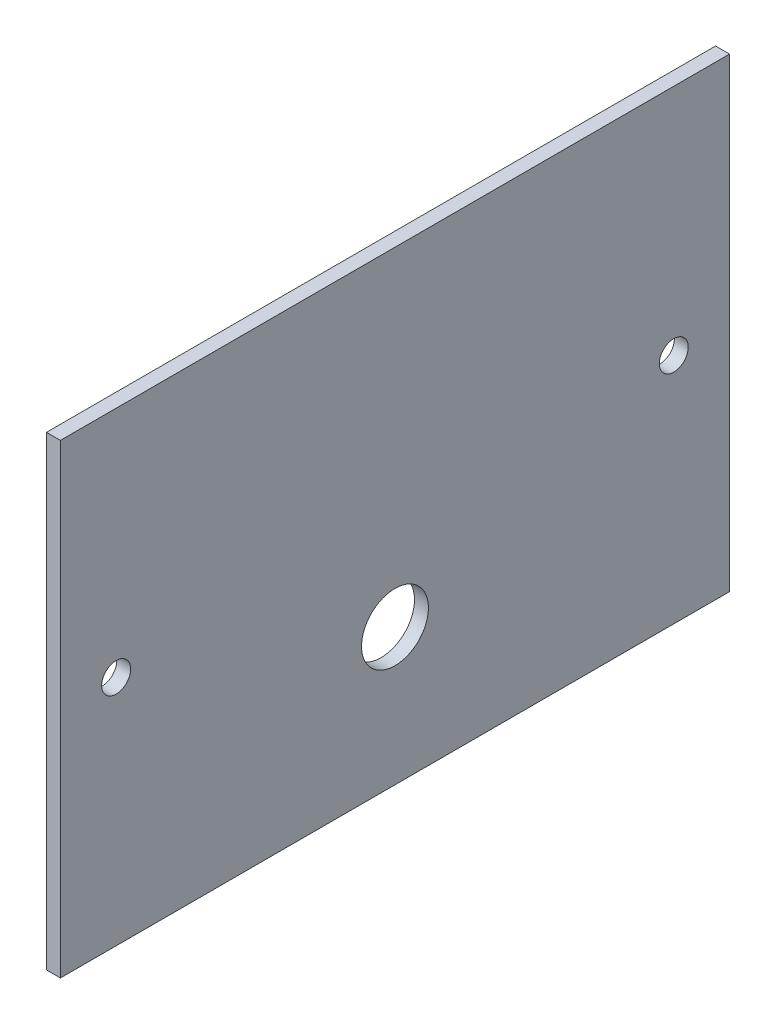
SolidWorks part; units mm, degrees
ref_plane "Front" through (0, 0, 0) normal (0, 0, 1) x (1, 0, 0)
ref_plane "Top" through (0, 0, 0) normal (0, 1, 0) x (1, 0, 0)
ref_plane "Right" through (0, 0, 0) normal (1, 0, 0) x (0, 0, -1)
sketch "Sketch1" plane through (0, 0, 0) normal (1, 0, 0) x (0, 0, -1)
  line L0 (25.4, 106.045) -> (25.4, 0) construction
  line L1 (0, 0) -> (152.4, 0)
  line L2 (0, 0) -> (0, 106.045)
  line L3 (0, 106.045) -> (152.4, 106.045)
  line L4 (152.4, 0) -> (152.4, 106.045)
  line L5 (152.4, 28.575) -> (0, 28.575) construction
  dimension "D1" = 152.4
  dimension "D2" = 106.045
  dimension "D4" = 28.575
extrude "Boss-Extrude1" add sketch "Sketch1" along normal blind 3.175
sketch "Sketch2" plane through (3.175, 0, 0) normal (1, 0, 0) x (0, 0, -1)
  line L0 (0, 0) -> (152.4, 0) construction
  line L1 (152.4, 106.045) -> (0, 106.045) construction
  line L2 (152.4, 0) -> (152.4, 106.045) construction
  line L3 (0, 106.045) -> (0, 0) construction
  line L4 (76.2, 31.115) -> (76.2, 106.045) construction
  circle A0 centre (76.2, 31.115) radius 7.62
  circle A1 centre (12.7, 52.959) radius 3.302
  circle A2 centre (139.7, 52.959) radius 3.302
  point P15 (0, 0)
  dimension "D3" = 15.24
  dimension "D4" = 6.604
  dimension "D1" = 31.115
  dimension "D2" = 76.2
  dimension "D5" = 53.086
  dimension "D6" = 12.7
extrude "Cut-Extrude1" cut sketch "Sketch2" against normal through all
